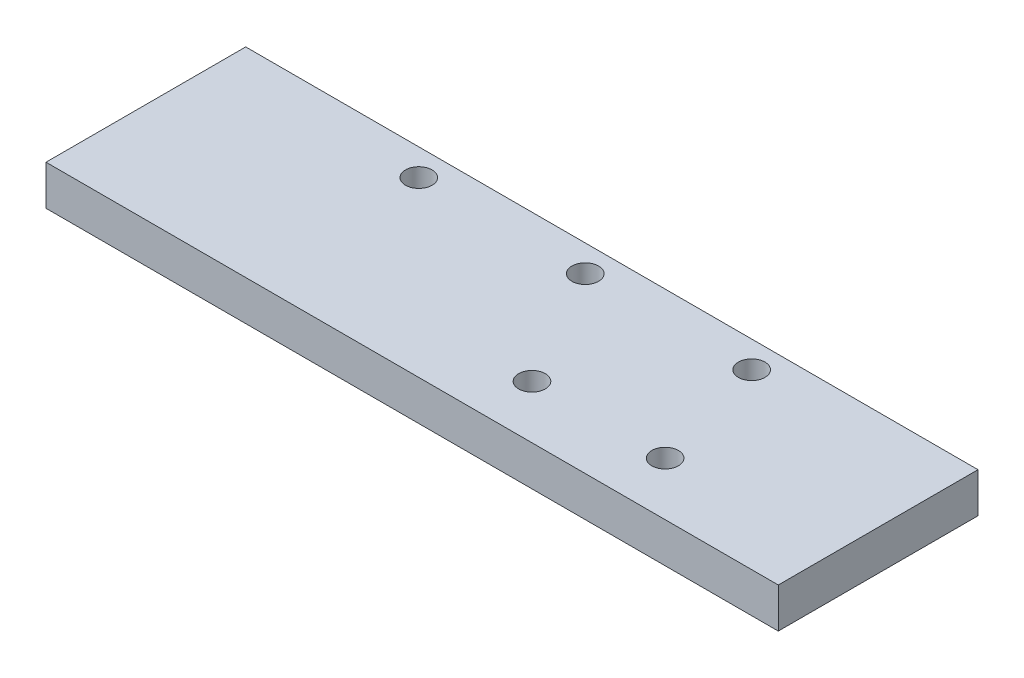
SolidWorks part; units mm, degrees
ref_plane "Front Plane" through (0, 0, 0) normal (0, 0, 1) x (1, 0, 0)
ref_plane "Top Plane" through (0, 0, 0) normal (0, 1, 0) x (1, 0, 0)
ref_plane "Right Plane" through (0, 0, 0) normal (1, 0, 0) x (0, 0, -1)
sketch "Sketch1" plane through (0, 0, 0) normal (0, 1, 0) x (1, 0, 0)
  line L1 (-102.5105, 65.1674) -> (7.4895, 65.1674)
  line L2 (-102.5105, 65.1674) -> (-102.5105, 35.1674)
  line L3 (-102.5105, 35.1674) -> (7.4895, 35.1674)
  line L4 (7.4895, 65.1674) -> (7.4895, 35.1674)
  dimension "D1" = 30
  dimension "D2" = 110
extrude "Boss-Extrude1" add sketch "Sketch1" along normal blind 6 contours L2 L3 L4 L1
sketch "Sketch2" plane through (0, 0, 0) normal (0, -1, 0) x (1, 0, 0)
  line L1 (-102.5105, -65.1674) -> (7.4895, -65.1674) construction
  line L2 (7.4895, -65.1674) -> (7.4895, -35.1674) construction
  line L3 (-102.5105, -35.1674) -> (7.4895, -35.1674) construction
  circle A0 centre (-72.5105, -61.1674) radius 2
  circle A1 centre (-47.5105, -61.1674) radius 2
  circle A2 centre (-22.5105, -61.1674) radius 2
  circle A9 centre (-17.5105, -43.1674) radius 2
  circle A10 centre (-37.5105, -43.1674) radius 2
  dimension "D1" = 30
  dimension "D5" = 25
  dimension "D7" = 25
  dimension "D9" = 20
  dimension "D2" = 4
  dimension "D3" = 25
  dimension "D4" = 4
  dimension "D6" = 4
  dimension "D8" = 8
  dimension "D10" = 8
extrude "Cut-Extrude1" cut sketch "Sketch2" against normal blind 10
